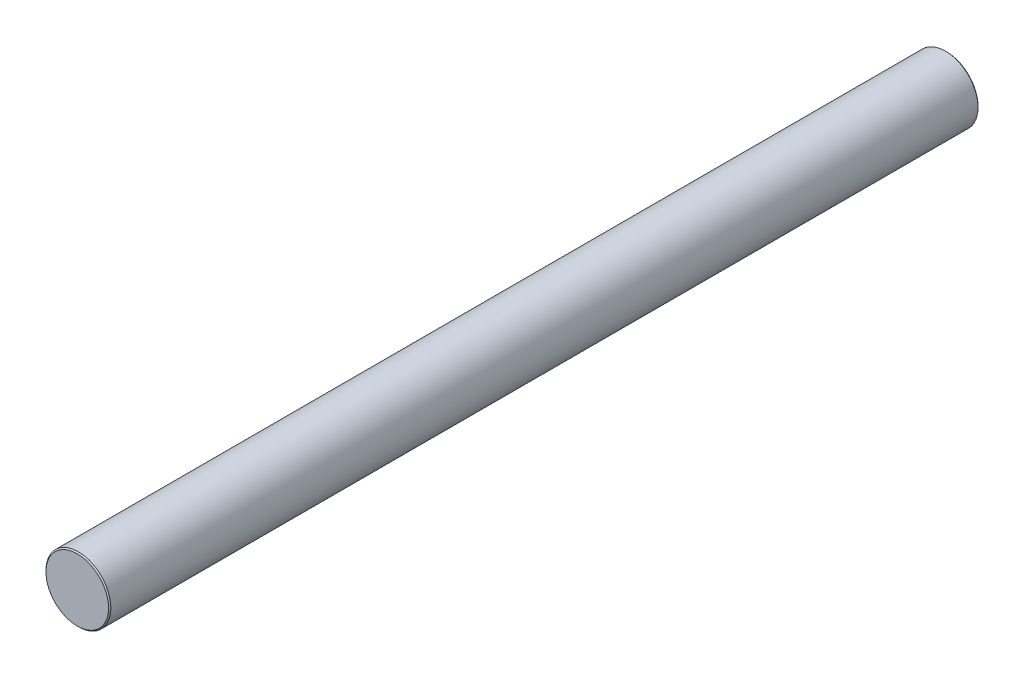
SolidWorks part; units mm, degrees
material "Chrome Stainless Steel"
ref_plane "Ön Düzlem" through (0, 0, 0) normal (0, 0, 1) x (1, 0, 0)
ref_plane "Üst Düzlem" through (0, 0, 0) normal (0, 1, 0) x (1, 0, 0)
ref_plane "Sağ Düzlem" through (0, 0, 0) normal (1, 0, 0) x (0, 0, -1)
sketch "Sketch1" plane through (0, 0, 0) normal (0, 0, 1) x (1, 0, 0)
  circle A0 centre (0, 0) radius 28
extrude "Boss-Extrude1" add sketch "Sketch1" along normal mid plane 750
chamfer "Chamfer1" distance 1 angle 45 2 edges at (28, 0, -375) (28, 0, 375)
